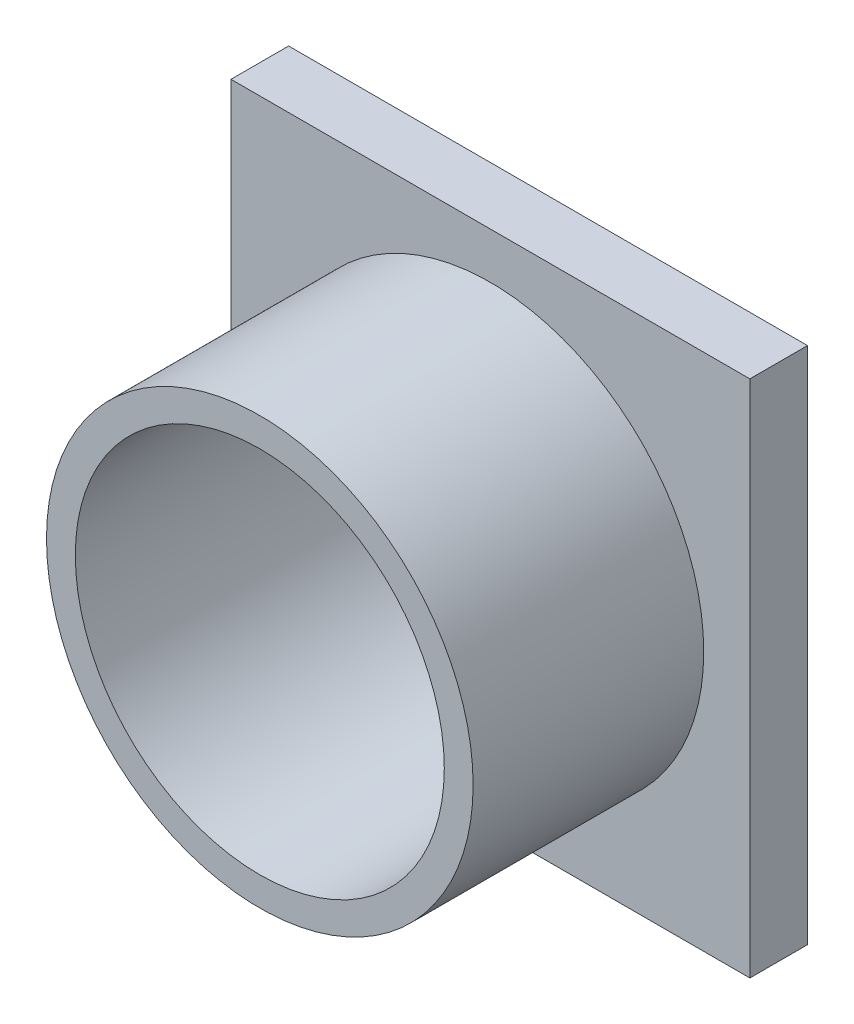
SolidWorks part; units mm, degrees
ref_plane "Plan de face" through (0, 0, 0) normal (0, 0, 1) x (1, 0, 0)
ref_plane "Plan de dessus" through (0, 0, 0) normal (0, 1, 0) x (1, 0, 0)
ref_plane "Plan de droite" through (0, 0, 0) normal (1, 0, 0) x (0, 0, -1)
sketch "Esquisse1" plane through (0, 0, 0) normal (0, 0, 1) x (1, 0, 0)
  line L1 (-22.5, 22.5) -> (22.5, 22.5)
  line L2 (-22.5, 22.5) -> (-22.5, -22.5)
  line L3 (-22.5, -22.5) -> (22.5, -22.5)
  line L4 (22.5, 22.5) -> (22.5, -22.5)
  line L5 (-22.5, 22.5) -> (22.5, -22.5) construction
  line L6 (-22.5, -22.5) -> (22.5, 22.5) construction
  circle A0 centre (0, 0) radius 16
  point P0 (0, 0)
  dimension "D1" = 32
  dimension "D2" = 45
  dimension "D3" = 45
extrude "Boss.-Extru.1" add sketch "Esquisse1" along normal blind 5
sketch "Esquisse2" plane through (0, 0, 5) normal (0, 0, 1) x (1, 0, 0)
  circle A0 centre (0, 0) radius 16
  circle A1 centre (0, 0) radius 18.5
  dimension "D1" = 32
  dimension "D2" = 37
extrude "Boss.-Extru.2" add sketch "Esquisse2" along normal blind 20
sketch "Esquisse3" plane through (0, 0, 0) normal (0, 0, -1) x (-1, 0, 0)
  line L0 (0, 22.5) -> (0, -22.5) construction
  line L1 (-22.5, 22.5) -> (22.5, 22.5) construction
  line L2 (22.5, -22.5) -> (-22.5, -22.5) construction
  line L3 (-22.5, 0) -> (22.5, 0) construction
  line L4 (-22.5, -22.5) -> (-22.5, 22.5) construction
  line L5 (22.5, 22.5) -> (22.5, -22.5) construction
  line L6 (14, 19) -> (14, 15)
  line L7 (-19, 19) -> (-14, 19)
  line L8 (-19, 19) -> (-19, 15)
  line L9 (-19, 15) -> (-14, 15)
  line L10 (-14, 19) -> (-14, 15)
  line L11 (-19, 19) -> (-14, 15) construction
  line L12 (-19, 15) -> (-14, 19) construction
  line L13 (19, 15) -> (14, 15)
  line L14 (19, 19) -> (19, 15)
  line L15 (19, 19) -> (14, 19)
  line L16 (-14, -19) -> (-14, -15)
  line L17 (-19, -15) -> (-14, -15)
  line L18 (-19, -19) -> (-19, -15)
  line L19 (-19, -19) -> (-14, -19)
  line L20 (19, -19) -> (14, -19)
  line L21 (19, -19) -> (19, -15)
  line L22 (19, -15) -> (14, -15)
  line L23 (14, -19) -> (14, -15)
  point P12 (-16.5, 17)
  dimension "D1" = 5
  dimension "D2" = 4
  dimension "D3" = 3.5
  dimension "D4" = 3.5
extrude "Boss.-Extru.3" add sketch "Esquisse3" along normal blind 3
